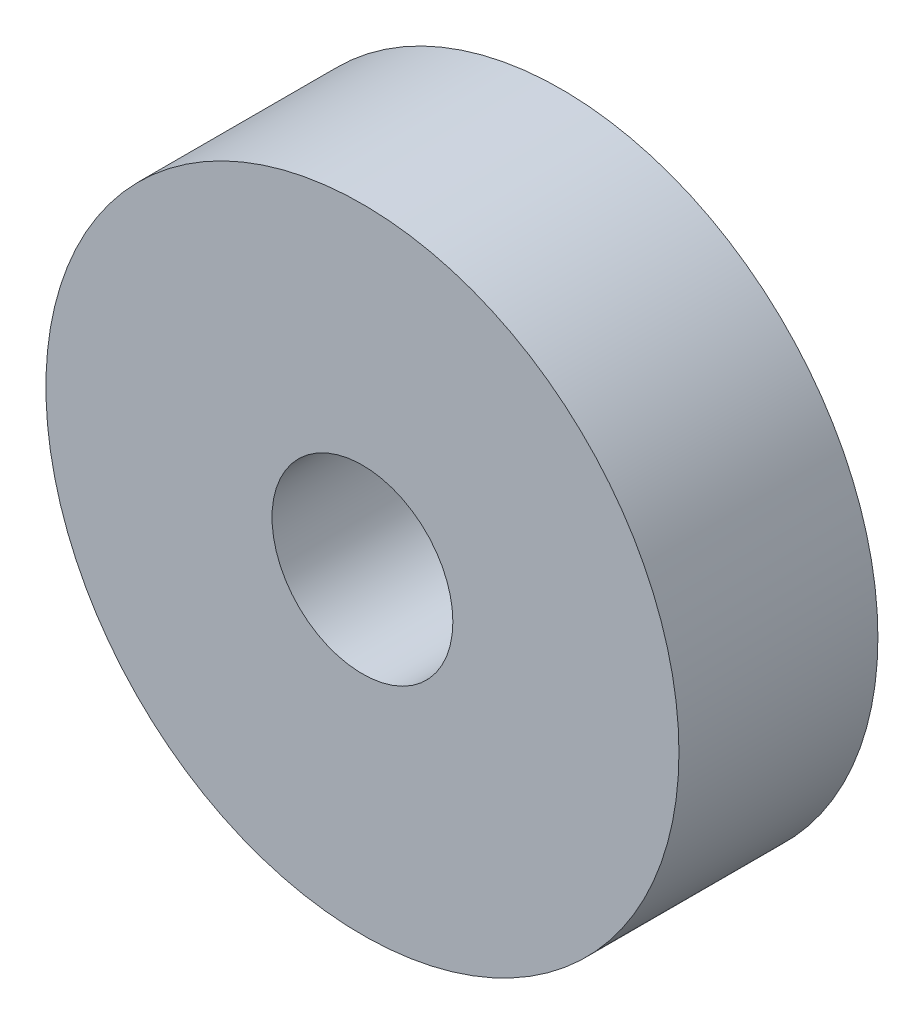
SolidWorks part; units mm, degrees
ref_plane "Alzado" through (0, 0, 0) normal (0, 0, 1) x (1, 0, 0)
ref_plane "Planta" through (0, 0, 0) normal (0, 1, 0) x (1, 0, 0)
ref_plane "Vista lateral" through (0, 0, 0) normal (1, 0, 0) x (0, 0, -1)
sketch "Croquis1" plane through (0, 0, 0) normal (0, 0, 1) x (1, 0, 0)
  circle A0 centre (0, 0) radius 17.5
  circle A1 centre (0, 0) radius 5
  dimension "D1" = 10
  dimension "D2" = 35
extrude "Saliente-Extruir1" add sketch "Croquis1" along normal blind 11
